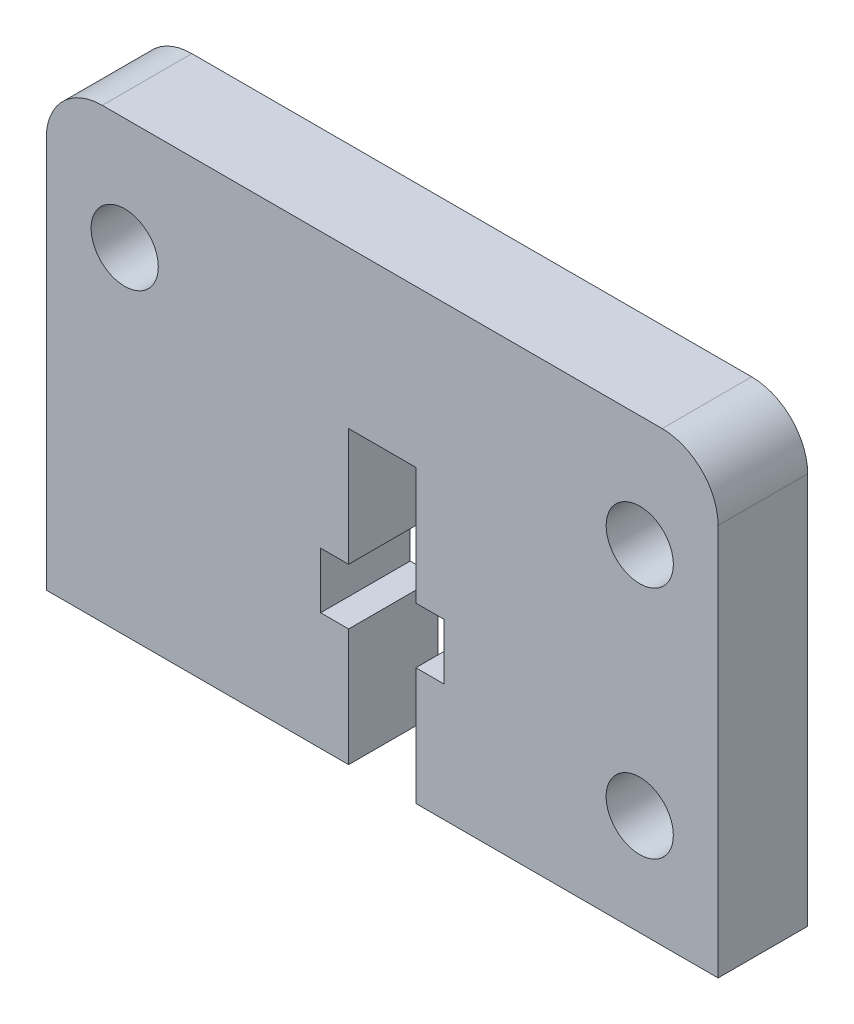
SolidWorks part; units mm, degrees
ref_plane "Спереди" through (0, 0, 0) normal (0, 0, 1) x (1, 0, 0)
ref_plane "Сверху" through (0, 0, 0) normal (0, 1, 0) x (1, 0, 0)
ref_plane "Справа" through (0, 0, 0) normal (1, 0, 0) x (0, 0, -1)
sketch "Эскиз1" plane through (0, 0, 0) normal (0, 0, 1) x (1, 0, 0)
  line L0 (15, 20) -> (15, 0) construction
  line L1 (0, 0) -> (30, 0)
  line L2 (0, 0) -> (0, 17.5)
  line L3 (2.5, 20) -> (27.5, 20)
  line L4 (30, 0) -> (30, 17.5)
  line L5 (30.85, 9.76) -> (0.85, 9.76) construction
  circle A0 centre (3.5, 15) radius 1.5
  circle A2 centre (26.5, 15) radius 1.5
  circle A3 centre (26.5, 4.52) radius 1.5
  arc A6 (27.5, 20) -> (30, 17.5) centre (27.5, 17.5) cw
  arc A7 (2.5, 20) -> (0, 17.5) centre (2.5, 17.5) ccw
  point P17 (0, 20)
  point P19 (30, 20)
  point P20 (30, 20)
  point P21 (0, 20)
  dimension "D3" = 3
  dimension "D4" = 23
  dimension "D5" = 5.24
  dimension "D6" = 5
  dimension "D7" = 2.5
  dimension "D8" = 2.5
  dimension "D9" = 10.48
  dimension "D1" = 30
  dimension "D2" = 20
extrude "Бобышка-Вытянуть1" add sketch "Эскиз1" along normal blind 4
sketch "Эскиз2" plane through (0, 0, 4) normal (0, 0, 1) x (1, 0, 0)
  line L0 (13.5, 0) -> (13.5, 5.25)
  line L1 (0, 0) -> (30, 0) construction
  line L2 (13.5, 5.25) -> (12.25, 5.25)
  line L3 (12.25, 5.25) -> (12.25, 7.75)
  line L4 (12.25, 7.75) -> (13.5, 7.75)
  line L5 (13.5, 7.75) -> (13.5, 13)
  line L6 (13.5, 13) -> (16.5, 13)
  line L7 (15, 13) -> (15, 0) construction
  line L8 (16.5, 5.25) -> (17.75, 5.25)
  line L9 (16.5, 0) -> (16.5, 5.25)
  line L10 (17.75, 5.25) -> (17.75, 7.75)
  line L11 (17.75, 7.75) -> (16.5, 7.75)
  line L12 (16.5, 7.75) -> (16.5, 13)
  dimension "D1" = 3
  dimension "D2" = 13
  dimension "D3" = 2.5
  dimension "D4" = 5.5
extrude "Вырез-Вытянуть1" cut sketch "Эскиз2" against normal blind 4 and the other way through all
